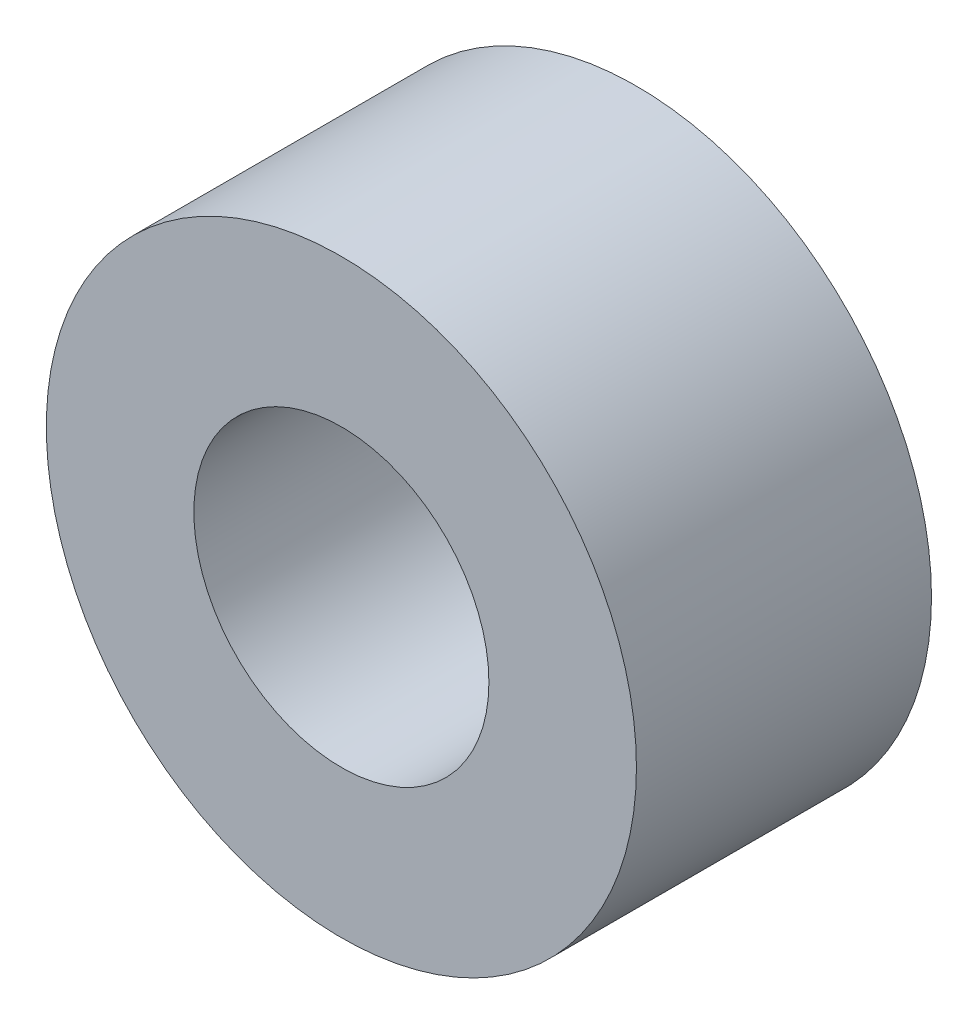
SolidWorks part; units mm, degrees
ref_plane "前视基准面" through (0, 0, 0) normal (0, 0, 1) x (1, 0, 0)
ref_plane "上视基准面" through (0, 0, 0) normal (0, 1, 0) x (1, 0, 0)
ref_plane "右视基准面" through (0, 0, 0) normal (1, 0, 0) x (0, 0, -1)
sketch "草图1" plane through (0, 0, 0) normal (0, 0, 1) x (1, 0, 0)
  circle A0 centre (0, 0) radius 5
  circle A1 centre (0, 0) radius 10
  dimension "D1" = 10
  dimension "D2" = 20
extrude "凸台-拉伸1" add sketch "草图1" along normal blind 10
